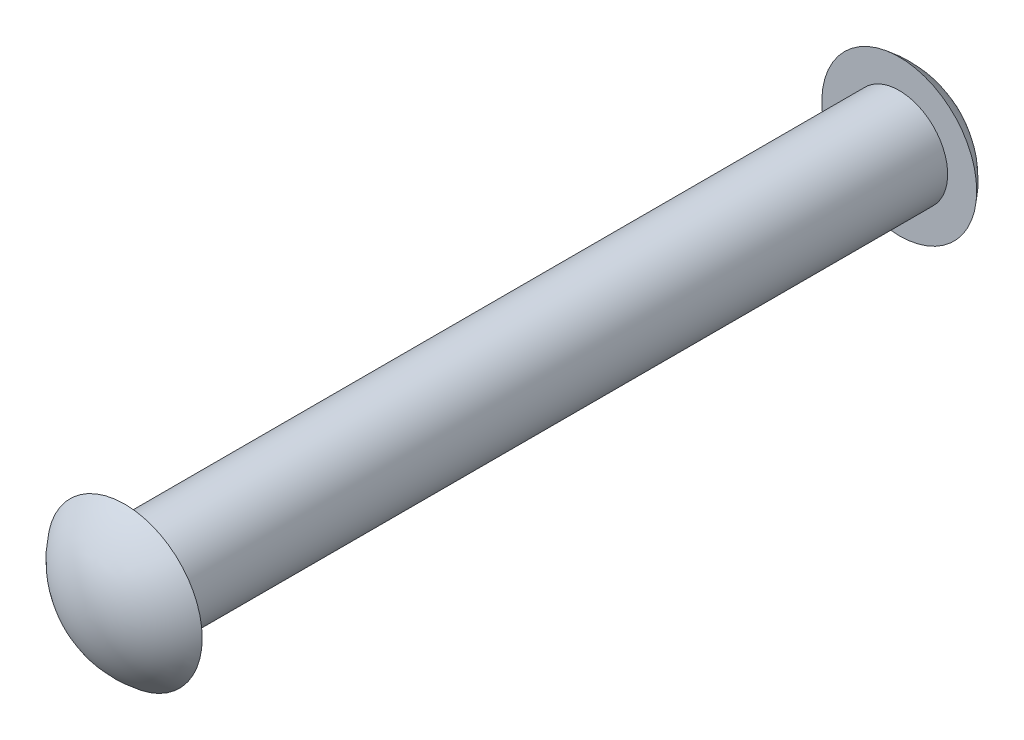
SolidWorks part; units mm, degrees
ref_plane "Front Plane" through (0, 0, 0) normal (0, 0, 1) x (1, 0, 0)
ref_plane "Top Plane" through (0, 0, 0) normal (0, 1, 0) x (1, 0, 0)
ref_plane "Right Plane" through (0, 0, 0) normal (1, 0, 0) x (0, 0, -1)
sketch "Sketch2" plane through (0, 0, 0) normal (0, 0, 1) x (1, 0, 0)
  circle A0 centre (0, 0) radius 3.175
  dimension "D1" = 6.35
extrude "Boss-Extrude1" add sketch "Sketch2" along normal blind 50.8
ref_plane "Plane2" through (0, 0, 25.4) normal (0, 0, 1) x (1, 0, 0)
ref_axis "Axis1" through (0, 0, 50.8) along (0, 0, -1)
sketch "Sketch6" plane through (0, 0, 0) normal (1, 0, 0) x (0, 0, -1)
  line L0 (-50.8, 0) -> (-50.8, 5.08)
  line L1 (-50.8, 3.175) -> (-50.8, -3.175) construction
  line L2 (-50.8, 0) -> (-53.34, 0)
  line L3 (-25.4, 0) -> (-25.4, 4.7891) construction
  line L4 (-25.4, 3.4925) -> (-25.4, -3.4925) construction
  line L5 (0, 0) -> (2.54, 0)
  line L6 (0, 0) -> (0, 5.08)
  arc A0 (-53.34, 0) -> (-50.8, 5.08) centre (-46.99, 0) cw
  arc A1 (2.54, 0) -> (0, 5.08) centre (-3.81, 0) ccw
  dimension "D1" = 5.08
  dimension "D2" = 2.54
revolve "Revolve2" add sketch "Sketch6" angle 360 about axis through (0, 0, 50.8) along (0, 0, -1)
